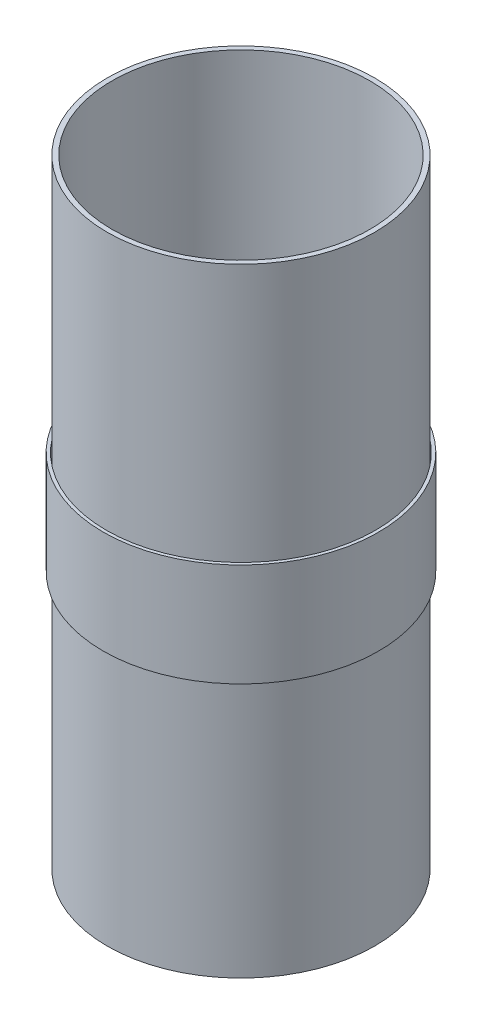
SolidWorks part; units mm, degrees
material "E-Glass Fiber"
ref_plane "Front Plane" through (0, 0, 0) normal (0, 0, 1) x (1, 0, 0)
ref_plane "Top Plane" through (0, 0, 0) normal (0, 1, 0) x (1, 0, 0)
ref_plane "Right Plane" through (0, 0, 0) normal (1, 0, 0) x (0, 0, -1)
sketch "Sketch1" plane through (0, 0, 0) normal (0, 1, 0) x (1, 0, 0)
  circle A0 centre (0, 0) radius 47.6504
  circle A1 centre (0, 0) radius 49.4538
  dimension "D1" = 95.3008
  dimension "D2" = 98.9076
extrude "Boss-Extrude1" add sketch "Sketch1" along normal blind 228.6
sketch "Sketch2" plane through (0, 228.6, 0) normal (0, 1, 0) x (1, 0, 0)
  circle A0 centre (0, 0) radius 50.9524
  circle A1 centre (0, 0) radius 49.7967
  dimension "D1" = 101.9048
  dimension "D2" = 99.5934
extrude "Boss-Extrude2" add sketch "Sketch2" along normal blind 38.1 from offset 133.35 separate body
equation "\"4.5.00in\"=0"
